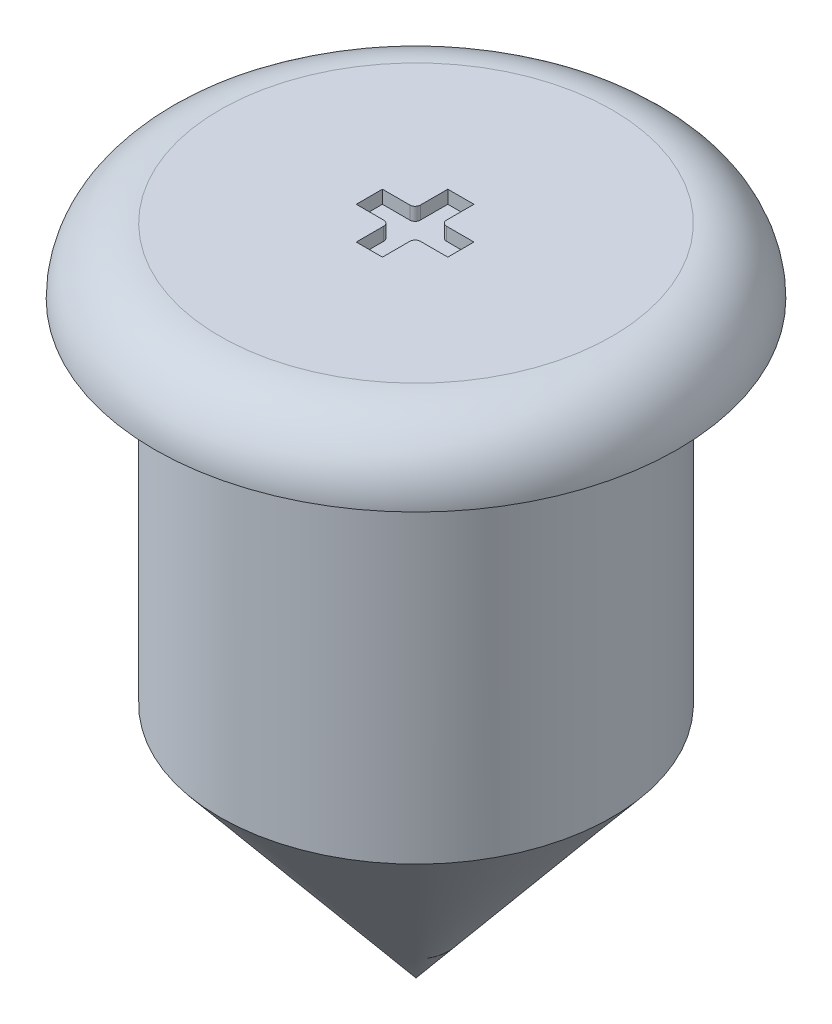
SolidWorks part; units mm, degrees
ref_plane "Front" through (0, 0, 0) normal (0, 0, 1) x (1, 0, 0)
ref_plane "Top" through (0, 0, 0) normal (0, 1, 0) x (1, 0, 0)
ref_plane "Right" through (0, 0, 0) normal (1, 0, 0) x (0, 0, -1)
sketch "Sketch1" plane through (0, 0, 0) normal (0, 0, 1) x (1, 0, 0)
  line L0 (0, -33.8274) -> (0, -28.8274)
  line L1 (0, -55) -> (0, 55) construction
  line L2 (1.5, -32.013) -> (1.5, -29.3274)
  line L3 (1.5, -29.3274) -> (2, -29.3274)
  line L4 (1.5, -28.8274) -> (0, -28.8274)
  line L5 (0, -33.8274) -> (1.5, -32.013)
  arc A0 (2, -29.3274) -> (1.5, -28.8274) centre (1.5, -29.3274) ccw
  dimension "D1" = 5
revolve "Revolve1" add sketch "Sketch1" angle 360 about L0
cosmetic thread "Cosmetic Thread1" parameters "D2"=2.439
sketch "Sketch2" plane through (0, -28.8274, 0) normal (0, 1, 0) x (1, 0, 0)
  line L0 (-0.1027, 0.3459) -> (0.0973, 0.3459)
  line L1 (0.0973, 0.3459) -> (0.0973, 0.1359)
  line L2 (0.1373, 0.0959) -> (0.3473, 0.0959)
  line L3 (0.3473, 0.0959) -> (0.3473, -0.1041)
  line L4 (0.3473, -0.1041) -> (0.1373, -0.1041)
  line L5 (0.0973, -0.1441) -> (0.0973, -0.3541)
  line L6 (0.0973, -0.3541) -> (-0.1027, -0.3541)
  line L7 (-0.0027, 0.3459) -> (-0.0027, -0.3541) construction
  line L8 (-0.1027, -0.1441) -> (-0.1027, -0.3541)
  line L9 (-0.3527, -0.1041) -> (-0.1427, -0.1041)
  line L10 (-0.3527, 0.0959) -> (-0.3527, -0.1041)
  line L11 (-0.1427, 0.0959) -> (-0.3527, 0.0959)
  line L12 (-0.1027, 0.3459) -> (-0.1027, 0.1359)
  arc A0 (0.0973, 0.1359) -> (0.1373, 0.0959) centre (0.1373, 0.1359) ccw
  arc A1 (0.1373, -0.1041) -> (0.0973, -0.1441) centre (0.1373, -0.1441) ccw
  arc A2 (-0.1427, -0.1041) -> (-0.1027, -0.1441) centre (-0.1427, -0.1441) cw
  arc A3 (-0.1027, 0.1359) -> (-0.1427, 0.0959) centre (-0.1427, 0.1359) cw
  dimension "D1" = 0.04
  dimension "D2" = 0.04
extrude "Cut-Extrude1" cut sketch "Sketch2" against normal blind 0.1
